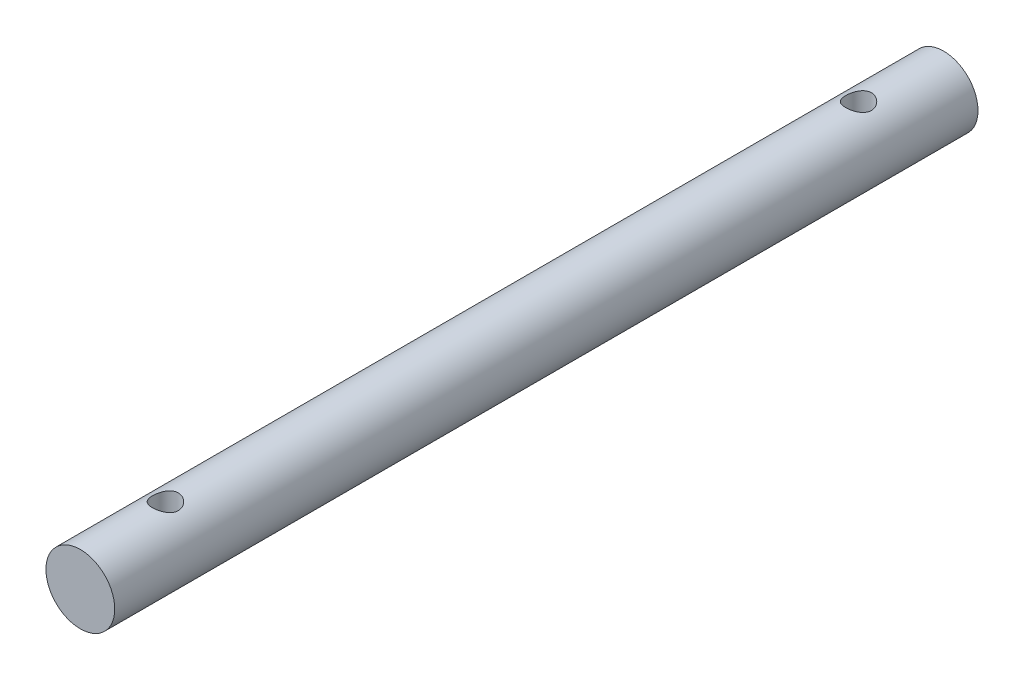
SolidWorks part; units mm, degrees
material "AISI 304"
ref_plane "Front Plane" through (0, 0, 0) normal (0, 0, 1) x (1, 0, 0)
ref_plane "Top Plane" through (0, 0, 0) normal (0, 1, 0) x (1, 0, 0)
ref_plane "Right Plane" through (0, 0, 0) normal (1, 0, 0) x (0, 0, -1)
sketch "Sketch2" plane through (0, 0, 0) normal (0, 0, 1) x (1, 0, 0)
  circle A0 centre (0, 0) radius 4
  dimension "D1" = 8
extrude "Boss-Extrude1" add sketch "Sketch2" along normal mid plane 100.36
sketch "Sketch3" plane through (0, 0, 0) normal (0, 1, 0) x (1, 0, 0)
  line L0 (0, 0) -> (17.158, 0) construction
  line L1 (4, 50.18) -> (-4, 50.18) construction
  circle A0 centre (0, 40.29) radius 1.5
  circle A1 centre (0, -40.29) radius 1.5
  dimension "D1" = 9.89
  dimension "D2" = 3
extrude "Cut-Extrude1" cut sketch "Sketch3" against normal through all both and the other way through all
